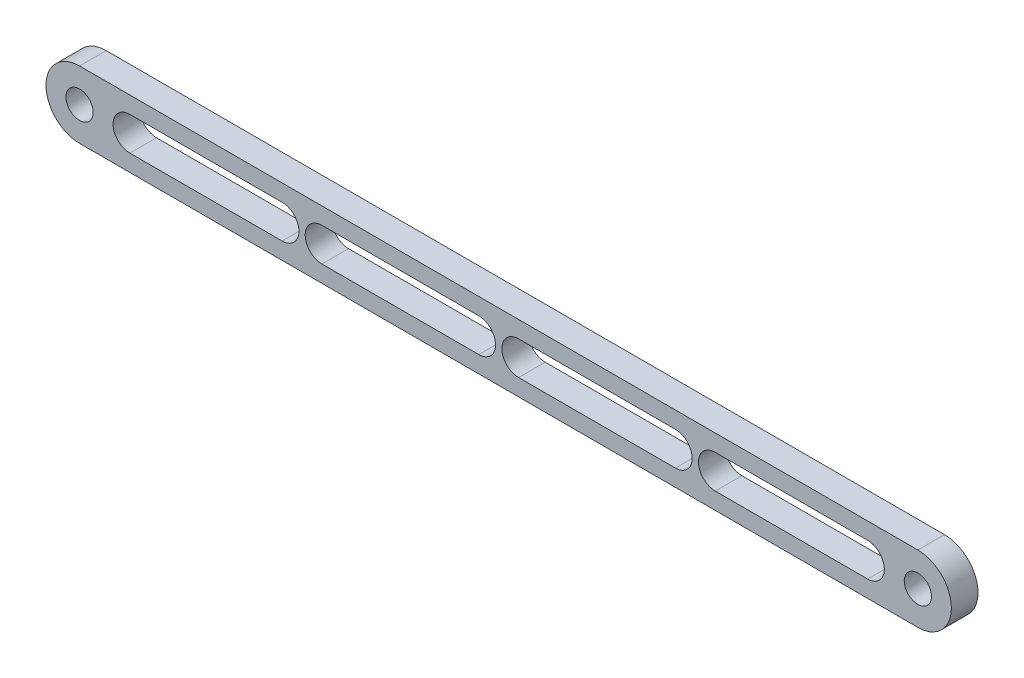
SolidWorks part; units mm, degrees
ref_plane "Front Plane" through (0, 0, 0) normal (0, 0, 1) x (1, 0, 0)
ref_plane "Top Plane" through (0, 0, 0) normal (0, 1, 0) x (1, 0, 0)
ref_plane "Right Plane" through (0, 0, 0) normal (1, 0, 0) x (0, 0, -1)
ref_plane "Plane1" through (0, 0, 6.35) normal (0, 0, 1) x (1, 0, 0)
sketch "Sketch1" plane through (0, 0, 6.35) normal (0, 0, 1) x (1, 0, 0)
  line L0 (104.75, 4) -> (142.1609, 4)
  line L1 (142.1609, -4) -> (104.75, -4)
  line L2 (12, 4) -> (48.3391, 4)
  line L3 (48.3391, -4) -> (12, -4)
  line L4 (57.8391, 4) -> (95.25, 4)
  line L5 (95.25, -4) -> (57.8391, -4)
  line L6 (188, -4) -> (151.6609, -4)
  line L7 (151.6609, 4) -> (188, 4)
  line L8 (200, 8) -> (0, 8)
  line L9 (0, -8) -> (200, -8)
  circle A0 centre (200, 0) radius 3.25
  circle A1 centre (0, 0) radius 3.25
  arc A2 (142.1609, 4) -> (142.1609, -4) centre (142.1609, 0) cw
  arc A3 (104.75, -4) -> (104.75, 4) centre (104.75, 0) cw
  arc A4 (48.3391, 4) -> (48.3391, -4) centre (48.3391, 0) cw
  arc A5 (12, -4) -> (12, 4) centre (12, 0) cw
  arc A6 (95.25, 4) -> (95.25, -4) centre (95.25, 0) cw
  arc A7 (57.8391, -4) -> (57.8391, 4) centre (57.8391, 0) cw
  arc A8 (188, 4) -> (188, -4) centre (188, 0) cw
  arc A9 (151.6609, -4) -> (151.6609, 4) centre (151.6609, 0) cw
  arc A10 (0, 8) -> (0, -8) centre (0, 0) ccw
  arc A11 (200, -8) -> (200, 8) centre (200, 0) ccw
extrude "Boss-Extrude1" add sketch "Sketch1" against normal blind 6.35
